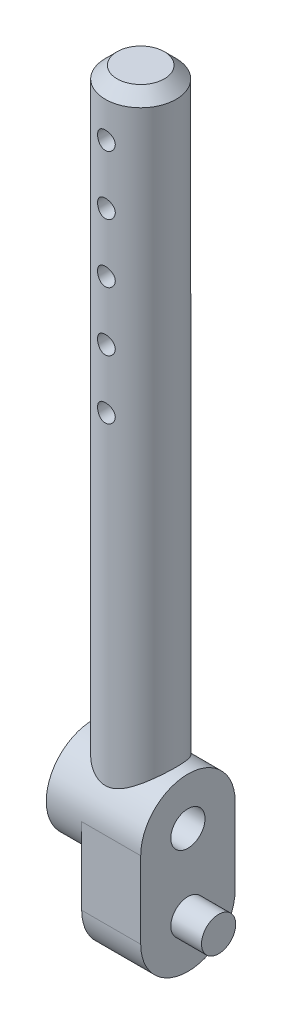
SolidWorks part; units mm, degrees
ref_plane "Front Plane" through (0, 0, 0) normal (0, 0, 1) x (1, 0, 0)
ref_plane "Top Plane" through (0, 0, 0) normal (0, 1, 0) x (1, 0, 0)
ref_plane "Right Plane" through (0, 0, 0) normal (1, 0, 0) x (0, 0, -1)
sketch "Sketch1" plane through (0, 0, 0) normal (1, 0, 0) x (0, 0, -1)
  line L0 (0, 0) -> (0, 6.5) construction
  line L1 (-4, 0) -> (-4, 6.5)
  line L2 (4, 0) -> (4, 6.5)
  arc A0 (-4, 0) -> (4, 0) centre (0, 0) ccw
  arc A1 (4, 6.5) -> (-4, 6.5) centre (0, 6.5) ccw
  circle A2 centre (0, 6.5) radius 1.45
  point P3 (0, 3.25)
  dimension "D2" = 14.5
  dimension "D3" = 2.9
  dimension "D1" = 8
extrude "Boss-Extrude1" add sketch "Sketch1" along normal blind 5
sketch "Sketch2" plane through (5, 0, 0) normal (1, 0, 0) x (0, 0, -1)
  line L0 (0, 0.05) -> (0, 2.3232) construction
  line L1 (4, 0) -> (4, 6.5) construction
  line L2 (-4, 6.5) -> (-4, 0) construction
  circle A0 centre (0, 0.05) radius 1.45
  arc A1 (-4, 0) -> (4, 0) centre (0, 0) ccw construction
  dimension "D1" = 2.9
  dimension "D2" = 2.6
extrude "Boss-Extrude2" add sketch "Sketch2" along normal blind 2.6
sketch "Sketch3" plane through (0, 0, 0) normal (-1, 0, 0) x (0, 0, 1)
  circle A0 centre (0, 6.5) radius 4
  circle A1 centre (0, 6.5) radius 4
  arc M3 (4, 6.5) -> (-4, 6.5) centre (0, 6.5) ccw
  circle M5 centre (0, 6.5) radius 1.45
extrude "Boss-Extrude3" add sketch "Sketch3" along normal blind 3 contours A0 M3 M5
sketch "Sketch5" plane through (0, 0, 0) normal (0, 0, 1) x (1, 0, 0)
  line L1 (1, 8) -> (4, 8)
  line L2 (1, 8) -> (1, 60.5)
  line L3 (1, 60.5) -> (4, 60.5)
  line L4 (4, 8) -> (4, 60.5)
  line L5 (1, 12.3381) -> (1, 18.0508) construction
  line L6 (-3, 10.5) -> (-3, 2.5) construction
  line L7 (5, 6.5) -> (5, 10.5) construction
  line L9 (5, 6.5) -> (0, 6.5) construction
  line L10 (1, 60.5) -> (1, 29.1135) construction
  dimension "D2" = 3
  dimension "D3" = 1.5
  dimension "D4" = 52.5
revolve "Revolve2" add sketch "Sketch5" angle 360 about L10
chamfer "Chamfer1" distance 1 angle 45 1 edges at (-2, 60.5, 0)
sketch "Sketch6" plane through (0, 0, 0) normal (0, 0, 1) x (1, 0, 0)
  line L0 (1, 59.1139) -> (1, 46.3179) construction
  line L1 (4, 59.5) -> (-2, 59.5) construction
  circle A0 centre (1, 56.5) radius 0.75
  circle A1 centre (1, 51.5) radius 0.75
  circle A2 centre (1, 46.5) radius 0.75
  circle A3 centre (1, 41.5) radius 0.75
  circle A4 centre (1, 36.5) radius 0.75
  dimension "D1" = 1.5
  dimension "D2" = 3
  dimension "D3" = 5
extrude "Cut-Extrude1" cut sketch "Sketch6" against normal through all both and the other way through all
